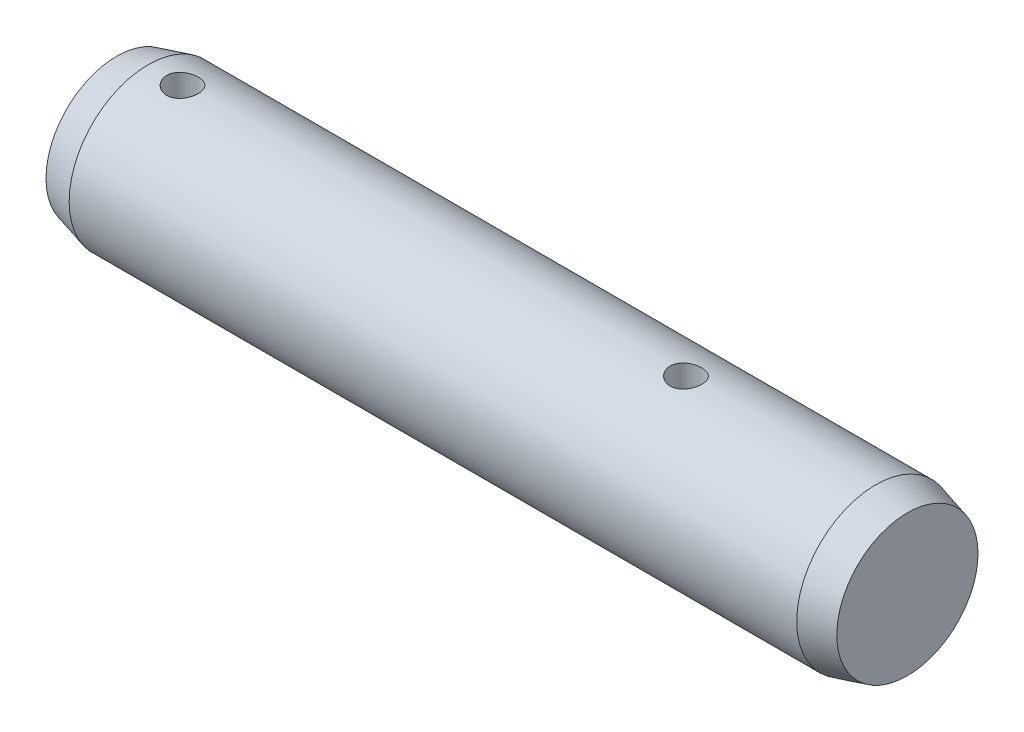
SolidWorks part; units mm, degrees
ref_plane "Front Plane" through (0, 0, 0) normal (0, 0, 1) x (1, 0, 0)
ref_plane "Top Plane" through (0, 0, 0) normal (0, 1, 0) x (1, 0, 0)
ref_plane "Right Plane" through (0, 0, 0) normal (1, 0, 0) x (0, 0, -1)
sketch "Sketch1" plane through (0, 0, 0) normal (0, 0, 1) x (1, 0, 0)
  line L0 (-13.8, 0) -> (13.8, 0) construction
  line L1 (13.8, 3) -> (13.8, -3) construction
  line L2 (-13.8, 3) -> (-13.8, -3) construction
  line L3 (15, 3) -> (15, -3) construction
  line L4 (-15, 3) -> (-15, -3) construction
  line L5 (-13.8, 0) -> (-15, 0) construction
  line L6 (13.8, 0) -> (15, 0) construction
  point P11 (9, 0)
  point P21 (-9, 0)
  dimension "Dia" = 6
  dimension "C" = 1.2
  dimension "D1" = 1.2
  dimension "Length" = 30
  dimension "D2" = 6
  dimension "D3" = 6
sketch "Sketch2" plane through (0, 0, 0) normal (1, 0, 0) x (0, 0, -1)
  circle A0 centre (0, 0) radius 3
extrude "Extrude1" add sketch "Sketch2" against normal up to vertex (13.8 mm away) and the other way up to vertex (13.8 mm away) up to point (-13.8, 3, 0) other way up to point (13.8, 3, 0)
sketch "Sketch3" plane through (13.8, 0, 0) normal (1, 0, 0) x (0, 0, -1)
  circle A1 centre (0, 0) radius 3
  circle A2 centre (0, 0) radius 3
  dimension "D1" = 0
extrude "Extrude2" add sketch "Sketch3" along normal up to vertex (1.2 mm away) draft 15 up to point (15, 0, 0)
sketch "Sketch4" plane through (-13.8, 0, 0) normal (-1, 0, 0) x (0, 0, 1)
  circle A1 centre (0, 0) radius 3
  circle A2 centre (0, 0) radius 3
  dimension "D1" = 0
extrude "Extrude3" add sketch "Sketch4" along normal up to vertex (1.2 mm away) draft 15 up to point (-15, 0, 0)
sketch "Sketch5" plane through (0, 0, 0) normal (1, 0, 0) x (0, 0, -1)
  line L0 (-3, 0) -> (3, 0) construction
  point P4 (0, 0)
  dimension "D1" = 6
sketch "Sketch6" plane through (0, 0, 0) normal (0, 1, 0) x (1, 0, 0)
  line L0 (-3.3, 0) -> (3.3, 0) construction
  line L1 (15, -2.6785) -> (15, 2.6785) construction
  line L2 (-15, 2.6785) -> (-15, -2.6785) construction
  circle A0 centre (6.6, 0) radius 0.6
  circle A1 centre (-12.5, 0) radius 0.6
  dimension "D1" = 1.2
  dimension "D3" = 2.5
  dimension "D2" = 8.4
extrude "Cut-Extrude1" cut sketch "Sketch6" against normal mid plane 10 contours A1
equation "\"D1@Sketch1\" = \"C@Sketch1\""
equation "\"D1@Sketch5\" = \"Dia@Sketch1\""
equation "\"D2@Sketch1\"=\"Dia@Sketch1\""
equation "\"D3@Sketch1\"=\"D2@Sketch1\""
